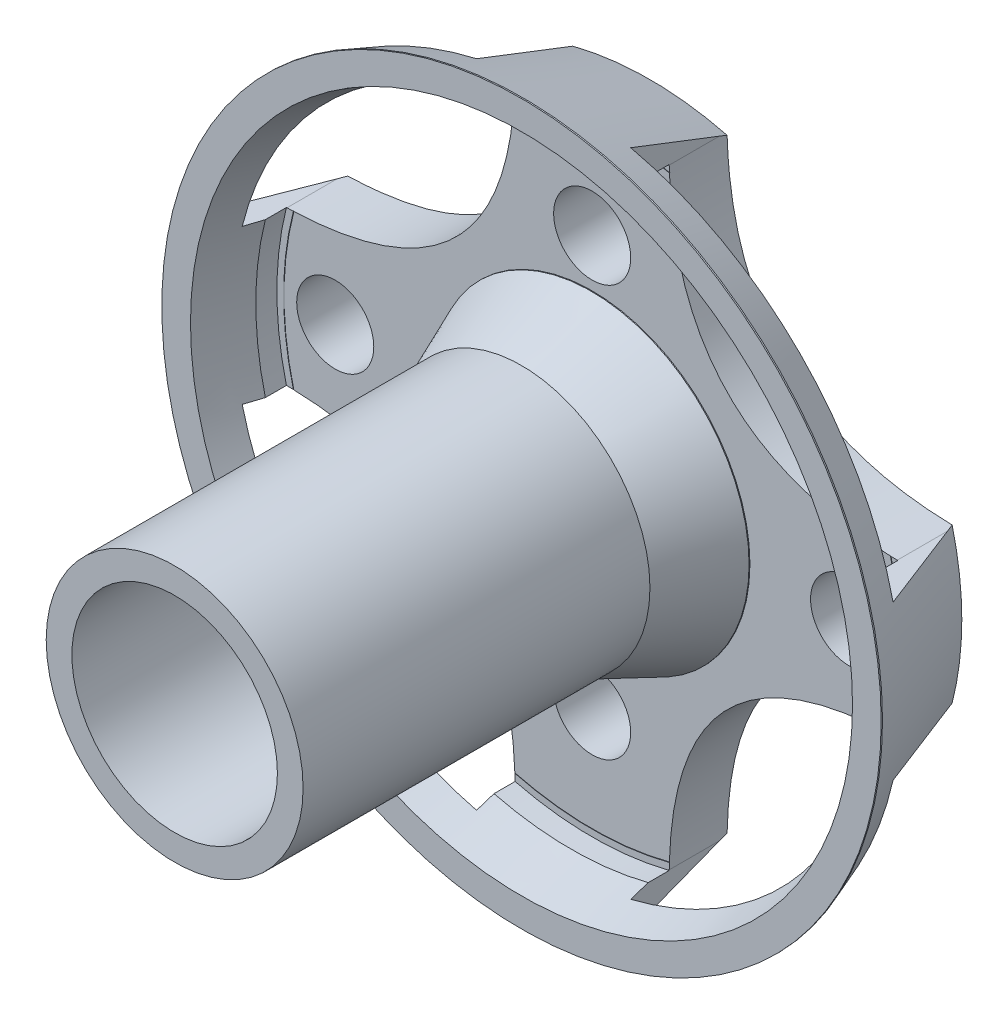
SolidWorks part; units mm, degrees
material "1060 Alloy"
ref_plane "Front Plane" through (0, 0, 0) normal (0, 0, 1) x (1, 0, 0)
ref_plane "Top Plane" through (0, 0, 0) normal (0, 1, 0) x (1, 0, 0)
ref_plane "Right Plane" through (0, 0, 0) normal (1, 0, 0) x (0, 0, -1)
sketch "Sketch1" plane through (0, 0, 0) normal (0, 0, 1) x (1, 0, 0)
  circle A0 centre (0, 0) radius 14
extrude "Boss-Extrude1" add sketch "Sketch1" along normal blind 18.5
sketch "Sketch2" plane through (0, 0, 18.5) normal (0, 0, 1) x (1, 0, 0)
  circle A0 centre (0, 0) radius 5
  circle A1 centre (0, 0) radius 4
  circle A2 centre (0, 0) radius 14.9574
  circle M2 centre (0, 0) radius 14
extrude "Cut-Extrude1" cut sketch "Sketch2" against normal blind 13.5 contours A0 M2
sketch "Sketch3" plane through (0, 0, 18.5) normal (0, 0, 1) x (1, 0, 0)
  circle A0 centre (0, 0) radius 4
extrude "Cut-Extrude2" cut sketch "Sketch3" against normal blind 22.5
sketch "Sketch5" plane through (0, 0, 0) normal (0, 0, -1) x (-1, 0, 0)
  circle A0 centre (0, 0) radius 7.5
  circle A1 centre (0, 0) radius 12.25
sketch "Sketch6" plane through (0, 0, 0) normal (1, 0, 0) x (0, 0, -1)
  line L0 (-4.9491, 14) -> (3.7776, 16.1996)
  line L1 (0, 14) -> (-5, 14) construction
  line L2 (-4.9491, 14) -> (5.0615, 10.2333)
  line L3 (3.7776, 16.1996) -> (5.0615, 10.2333)
  line L4 (-19.9218, 0) -> (0.8493, 0) construction
revolve "Cut-Revolve1" cut sketch "Sketch6" angle 360 about L4
sketch "Sketch7" plane through (0, 0, 0) normal (0, 0, -1) x (-1, 0, 0)
  line L4 (3, 15.6395) -> (3, 11.877)
  line L5 (3, 15.6395) -> (14.869, 14.3165)
  line L6 (14.869, 14.3165) -> (17.8611, 3)
  line L13 (11.877, 3) -> (17.8611, 3)
  circle A0 centre (0, 0) radius 12.25 construction
  circle A1 centre (0, 0) radius 7.5 construction
  spline S0 degree 2 poles (3, 11.877) (3.1211, 3.2066) (11.877, 3) knots 0 0 0 1 1 1
  point P0 (0, 0)
  point P6 (0, 0)
extrude "Cut-Extrude3" cut sketch "Sketch7" against normal blind 3.75
sketch "Sketch8" plane through (0, 0, 5) normal (0, 0, 1) x (1, 0, 0)
  circle A0 centre (0, 0) radius 6.1414
  circle A1 centre (0, 0) radius 12.2714
extrude "Cut-Extrude4" cut sketch "Sketch8" against normal blind 2.75
sketch "Sketch9" plane through (0, 0, 0) normal (0, 1, 0) x (1, 0, 0)
  line L0 (-12.0015, -2.2215) -> (-13.0015, -5.3691)
  line L1 (-13.0015, -5.3691) -> (-11.1551, -5.3691)
  line L2 (-11.1551, -5.3691) -> (-12.0015, -2.2215)
  line L3 (0, 1.7425) -> (0, 0) construction
  point P7 (-11.899, -2.25)
  point P8 (-12.0875, -2.4501)
  point P9 (-11.8876, -2.2221)
  point P10 (-12.0015, -2.2215)
revolve "Cut-Revolve2" cut sketch "Sketch9" angle 360 about L3
sketch "Sketch10" plane through (0, 0, 0) normal (0, 1, 0) x (1, 0, 0)
  line L0 (-5, -5) -> (-6.1414, -2.2831)
  line L1 (-6.1414, -2.25) -> (-6.1414, -5) construction
  line L2 (-6.1414, -2.2831) -> (-6.5723, -5.4132)
  line L3 (-6.5723, -5.4132) -> (-5, -5)
  line L4 (0, 0) -> (0, 2.3926) construction
  point P9 (-6.1414, -2.2831)
revolve "Cut-Revolve3" cut sketch "Sketch10" angle 360 about L4
pattern_circular "CirPattern1" count 4 every 90 about axis through (0, 0, 3.75) along (0, 0, 1) of "Cut-Extrude3"
sketch "Sketch11" plane through (0, 0, 0) normal (0, 0, -1) x (-1, 0, 0)
  circle A1 centre (0, 8) radius 1.5
  circle A2 centre (0, -8) radius 1.5
  circle A4 centre (-10, 0) radius 1.5
  circle A5 centre (10, 0) radius 1.5
extrude "Cut-Extrude5" cut sketch "Sketch11" against normal blind 3
